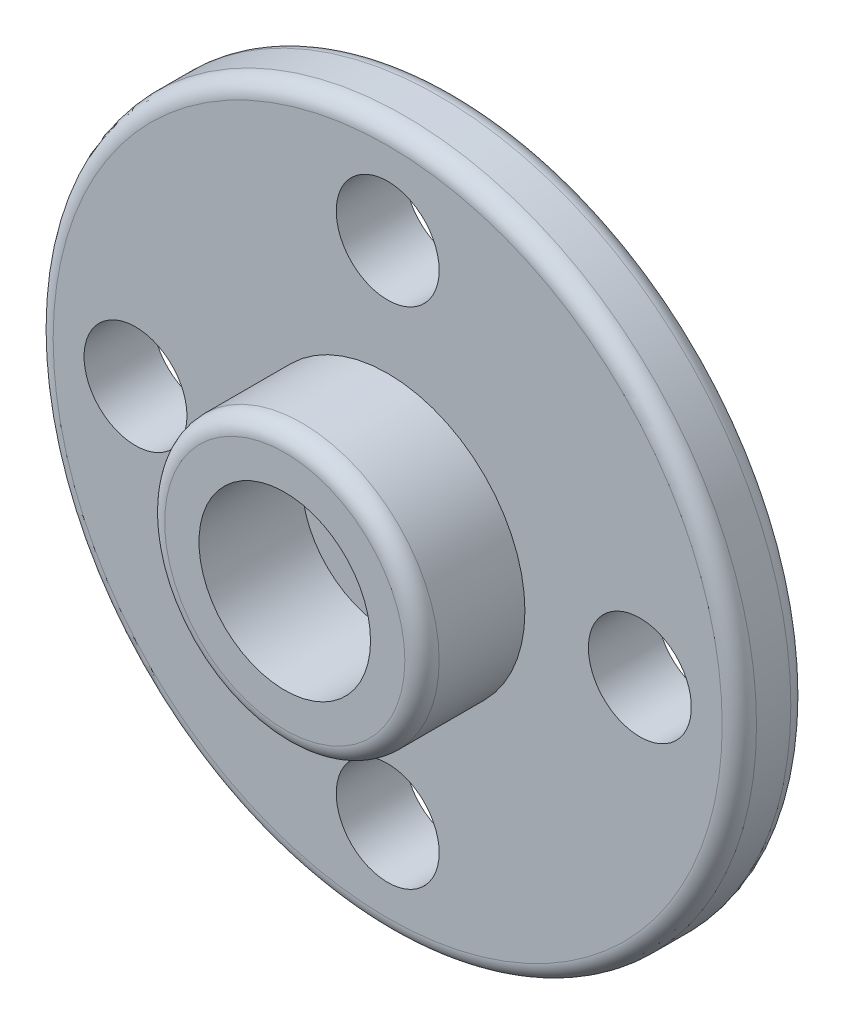
SolidWorks part; units mm, degrees
ref_plane "前视基准面" through (0, 0, 0) normal (0, 0, 1) x (1, 0, 0)
ref_plane "上视基准面" through (0, 0, 0) normal (0, 1, 0) x (1, 0, 0)
ref_plane "右视基准面" through (0, 0, 0) normal (1, 0, 0) x (0, 0, -1)
sketch "草图1" plane through (0, 0, 0) normal (0, 0, 1) x (1, 0, 0)
  line L0 (0, 52.1586) -> (0, -71.8542) construction
  line L1 (-7.35, 2.2455) -> (-7.35, -2.3503) construction
  line L2 (-67.4795, 0) -> (85.035, 0) construction
  line L3 (7.35, 2.6701) -> (7.35, -2.3503) construction
  line L4 (-2.4894, 7.35) -> (2.3597, 7.35) construction
  line L5 (-2.4894, -7.35) -> (2.3597, -7.35) construction
  circle A0 centre (0, 0) radius 10.25
  circle A1 centre (0, 0) radius 1.5
  circle A2 centre (-7.35, 0) radius 1.5
  circle A3 centre (7.35, 0) radius 1.5
  circle A4 centre (0, 7.35) radius 1.5
  circle A5 centre (7.35, 0) radius 1.5
  circle A6 centre (0, -7.35) radius 1.5
  point P25 (0, 0)
  dimension "D1" = 20.5
  dimension "D2" = 3
  dimension "D3" = 3
  dimension "D4" = 4
  dimension "D5" = 14.7
extrude "凸台-拉伸1" add sketch "草图1" along normal blind 2 contours A0 | A4 | A2 | A6 | A3 | A1
sketch "草图2" plane through (0, 0, 2) normal (0, 0, 1) x (1, 0, 0)
  circle A0 centre (0, 0) radius 4
  dimension "D1" = 8
extrude "凸台-拉伸2" add sketch "草图2" along normal blind 3
sketch "草图3" plane through (0, 0, 5) normal (0, 0, 1) x (1, 0, 0)
  circle A0 centre (0, 0) radius 2.5
  dimension "D1" = 5
extrude "切除-拉伸1" cut sketch "草图3" against normal blind 3
fillet "圆角1" radius 0.5 1 edges at (10.25, 0, 2)
fillet "圆角2" radius 0.5 1 edges at (10.25, 0, 0)
fillet "圆角3" radius 0.5 1 edges at (4, 0, 5)
